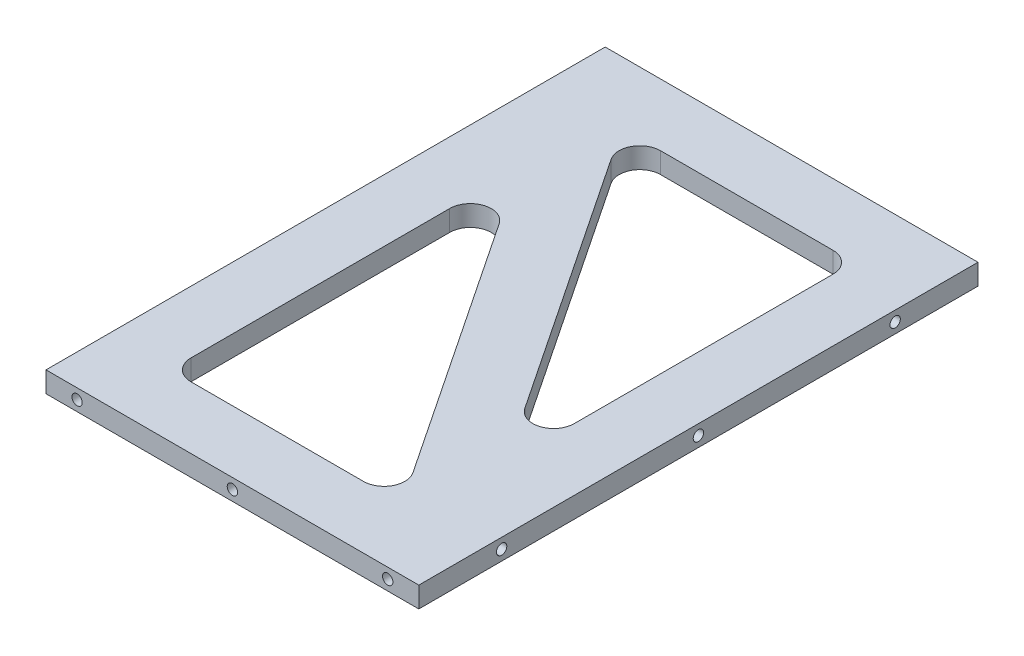
SolidWorks part; units mm, degrees
ref_plane "Front Plane" through (0, 0, 0) normal (0, 0, 1) x (1, 0, 0)
ref_plane "Top Plane" through (0, 0, 0) normal (0, 1, 0) x (1, 0, 0)
ref_plane "Right Plane" through (0, 0, 0) normal (1, 0, 0) x (0, 0, -1)
sketch "Sketch1" plane through (0, 0, 0) normal (0, 1, 0) x (1, 0, 0)
  line L1 (0, 0) -> (180, 0)
  line L2 (0, 0) -> (0, 270)
  line L3 (0, 270) -> (180, 270)
  line L4 (180, 0) -> (180, 270)
  dimension "D1" = 270
  dimension "D2" = 180
extrude "Boss-Extrude1" add sketch "Sketch1" along normal blind 10
sketch "Sketch2" plane through (0, 10, 0) normal (0, 1, 0) x (1, 0, 0)
  line L0 (0, 270) -> (180, 0) construction
  line L1 (38.0278, 240) -> (150, 240)
  line L2 (150, 240) -> (150, 72.0416)
  line L3 (150, 72.0416) -> (38.0278, 240)
  line L4 (30, 197.9584) -> (30, 30)
  line L5 (30, 30) -> (141.9722, 30)
  line L6 (141.9722, 30) -> (30, 197.9584)
  line L7 (0, 270) -> (0, 0) construction
  line L8 (0, 0) -> (180, 0) construction
  line L9 (180, 270) -> (0, 270) construction
  line L10 (180, 0) -> (180, 270) construction
  dimension "D1" = 15
  dimension "D2" = 15
  dimension "D3" = 30
  dimension "D4" = 30
  dimension "D5" = 30
  dimension "D6" = 30
extrude "Cut-Extrude1" cut sketch "Sketch2" against normal through all
fillet "Fillet1" radius 10 6 edges at (38.0278, 5, -240) (30, 5, -197.9584) (150, 5, -240) (150, 5, -72.0416) (141.9722, 5, -30) (30, 5, -30)
sketch "Sketch3" plane through (0, 0, -270) normal (0, 0, -1) x (-1, 0, 0)
  line L0 (-180, 10) -> (0, 10) construction
  line L1 (0, 10) -> (0, 0) construction
  line L2 (-180, 10) -> (-180, 0) construction
  circle A0 centre (-165, 5) radius 2.5
  circle A1 centre (-90, 5) radius 2.5
  circle A2 centre (-15, 5) radius 2.5
  point P8 (-90, 10)
  point P13 (-180, 5)
  dimension "D1" = 5
  dimension "D2" = 5
  dimension "D3" = 5
  dimension "D4" = 5
  dimension "D5" = 5
  dimension "D6" = 5
  dimension "D7" = 90
  dimension "D8" = 15
  dimension "D9" = 15
sketch "Sketch4" plane through (0, 0, 0) normal (0, 0, 1) x (1, 0, 0)
  line L0 (0, 10) -> (180, 10) construction
  line L2 (0, 10) -> (0, 0) construction
  line L3 (180, 10) -> (180, 0) construction
  circle A0 centre (15, 5) radius 2.5
  circle A1 centre (90, 5) radius 2.5
  circle A2 centre (165, 5) radius 2.5
  dimension "D1" = 5
  dimension "D2" = 5
  dimension "D3" = 5
  dimension "D4" = 5
  dimension "D5" = 5
  dimension "D6" = 5
  dimension "D7" = 15
  dimension "D8" = 90
  dimension "D9" = 15
hole_wizard "M6 Tapped Hole1" positions "Sketch5" profile "Sketch6" tap size "M6" standard "ISO"
sketch "Sketch5" plane through (0, 0, 0) normal (0, 0, 1) x (1, 0, 0)
  point P0 (15, 5)
  point P3 (90, 5)
  point P6 (165, 5)
sketch "Sketch6" plane through (15, 5, 0) normal (1, 0, 0) x (0, -1, 0)
  line L0 (0, 0) -> (0, 24.5022)
  line L1 (0, 24.5022) -> (2.5, 23)
  line L2 (2.5, 23) -> (2.5, 0)
  line L5 (2.5, 0) -> (0, 0)
  line L10 (0, 24.5022) -> (-2.5, 23) construction
  line L11 (0, -6.35) -> (0, 107.95) construction
  dimension "Tap Drill Dia." = 5
  dimension "Tap Drill Depth" = 23
  dimension "Drill Angle" = 118
cosmetic thread "Hole Thread1" parameters "D1"=17, "D2"=6
cosmetic thread "Hole Thread2" parameters "D1"=17, "D2"=6
cosmetic thread "Hole Thread3" parameters "D1"=17, "D2"=6
hole_wizard "M6 Tapped Hole2" positions "Sketch7" profile "Sketch8" tap size "M6" standard "ISO"
sketch "Sketch7" plane through (0, 0, -270) normal (0, 0, -1) x (-1, 0, 0)
  point P0 (-165, 5)
  point P3 (-90, 5)
  point P6 (-15, 5)
sketch "Sketch8" plane through (165, 5, -270) normal (1, 0, 0) x (0, 1, 0)
  line L0 (0, 0) -> (0, 21.5022)
  line L1 (0, 21.5022) -> (2.5, 20)
  line L2 (2.5, 20) -> (2.5, 0)
  line L5 (2.5, 0) -> (0, 0)
  line L10 (0, 21.5022) -> (-2.5, 20) construction
  line L11 (0, -6.35) -> (0, 107.95) construction
  dimension "Tap Drill Dia." = 5
  dimension "Tap Drill Depth" = 20
  dimension "Drill Angle" = 118
cosmetic thread "Hole Thread4" parameters "D1"=14, "D2"=6
cosmetic thread "Hole Thread5" parameters "D1"=14, "D2"=6
cosmetic thread "Hole Thread6" parameters "D1"=14, "D2"=6
sketch "Sketch9" plane through (180, 0, 0) normal (1, 0, 0) x (0, 0, -1)
  line L0 (0, 10) -> (270, 10) construction
  line L1 (270, 10) -> (270, 0) construction
  line L2 (0, 10) -> (0, 0) construction
  circle A0 centre (40, 5) radius 2.5
  circle A1 centre (135, 5) radius 2.5
  circle A2 centre (230, 5) radius 2.5
  dimension "D1" = 5
  dimension "D2" = 5
  dimension "D3" = 5
  dimension "D4" = 5
  dimension "D5" = 5
  dimension "D6" = 5
  dimension "D7" = 40
  dimension "D8" = 135
  dimension "D9" = 40
hole_wizard "M6 Tapped Hole3" positions "Sketch10" profile "Sketch11" tap size "M6" standard "ISO"
sketch "Sketch10" plane through (180, 0, 0) normal (1, 0, 0) x (0, 0, -1)
  point P0 (40, 5)
  point P3 (135, 5)
  point P6 (230, 5)
sketch "Sketch11" plane through (180, 5, -40) normal (0, 1, 0) x (0, 0, -1)
  line L0 (0, 0) -> (0, 21.5022)
  line L1 (0, 21.5022) -> (2.5, 20)
  line L2 (2.5, 20) -> (2.5, 0)
  line L5 (2.5, 0) -> (0, 0)
  line L10 (0, 21.5022) -> (-2.5, 20) construction
  line L11 (0, -6.35) -> (0, 107.95) construction
  dimension "Tap Drill Dia." = 5
  dimension "Tap Drill Depth" = 20
  dimension "Drill Angle" = 118
cosmetic thread "Hole Thread7" parameters "D1"=14, "D2"=6
cosmetic thread "Hole Thread8" parameters "D1"=14, "D2"=6
cosmetic thread "Hole Thread9" parameters "D1"=14, "D2"=6
